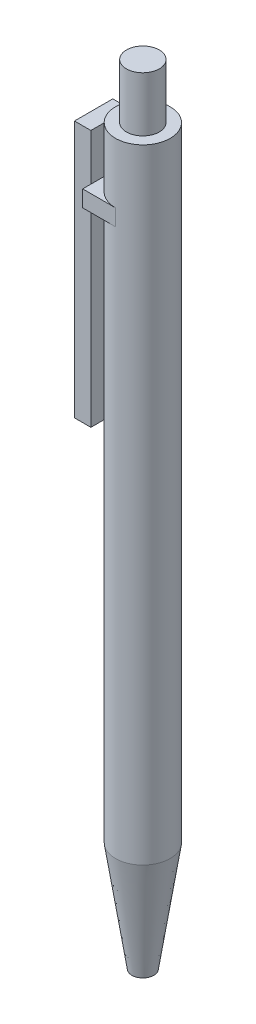
SolidWorks part; units mm, degrees
ref_plane "Plano frontal" through (0, 0, 0) normal (0, 0, 1) x (1, 0, 0)
ref_plane "Plano superior" through (0, 0, 0) normal (0, 1, 0) x (1, 0, 0)
ref_plane "Plano direito" through (0, 0, 0) normal (1, 0, 0) x (0, 0, -1)
sketch "Esboço2" plane through (0, 0, 0) normal (0, 0, 1) x (1, 0, 0)
  line L0 (-4.3308, 0) -> (2.3999, 0) construction
  line L1 (0, 22.7323) -> (0, -0.4304) construction
  line L2 (2, 0) -> (5, 20)
  line L3 (0, 0) -> (2, 0)
  line L4 (0, 20) -> (5, 20)
  line L5 (0, 20) -> (0, 0)
  point P9 (0, 0)
  point P11 (0, 0)
  dimension "D1" = 2
  dimension "D2" = 5
  dimension "D3" = 20
revolve "Revolução1" add sketch "Esboço2" angle 360 about L1
sketch "Esboço3" plane through (0, 20, 0) normal (0, 1, 0) x (1, 0, 0)
  line L0 (-21.4364, 0) -> (21.1711, 0) construction
  line L1 (0, 10.506) -> (0, -11.1957) construction
  circle A0 centre (0, 0) radius 5
  circle A1 centre (0, 0) radius 5 construction
  point P7 (0, 0)
  point P8 (0, 0)
extrude "Ressalto-extrusão1" add sketch "Esboço3" along normal blind 100
sketch "Esboço4" plane through (0, 120, 0) normal (0, 1, 0) x (1, 0, 0)
  line L0 (0, 11.0322) -> (0, -12.9913) construction
  line L1 (-16.4629, 0) -> (15.9617, 0) construction
  line L2 (-6, 5) -> (0, 5)
  line L3 (-6, 5) -> (-6, -5)
  line L4 (-6, -5) -> (0, -5)
  arc A0 (0, 5) -> (0, -5) centre (0, 0) cw
  circle A1 centre (0, 0) radius 5 construction
  point P8 (0, 0)
  point P10 (0, 0)
  point P15 (-6, 0)
  dimension "D1" = 6
extrude "Ressalto-extrusão2" add sketch "Esboço4" along normal blind 3
sketch "Esboço5" plane through (-6, 0, 0) normal (-1, 0, 0) x (0, 0, 1)
  line L0 (0, 126.2813) -> (0, 113.7617) construction
  line L1 (-5, 123) -> (5, 123) construction
  line L7 (-5, 123) -> (-5, 120) construction
  line L10 (-19.563, 121.5) -> (19.2509, 121.5) construction
  line L11 (-3.5, 131.5) -> (3.5, 131.5)
  line L12 (-3.5, 131.5) -> (-3.5, 84.5)
  line L13 (-3.5, 84.5) -> (3.5, 84.5)
  line L14 (3.5, 131.5) -> (3.5, 84.5)
  line L15 (-3.5, 131.5) -> (3.5, 84.5) construction
  line L16 (-3.5, 84.5) -> (3.5, 131.5) construction
  point P4 (0, 123)
  point P7 (0, 0)
  point P8 (-5, 121.5)
  point P9 (0, 121.5)
  point P11 (0, 108)
  dimension "D1" = 47
  dimension "D2" = 10
  dimension "D3" = 7
extrude "Ressalto-extrusão3" add sketch "Esboço5" along normal blind 3
sketch "Esboço6" plane through (0, 123, 0) normal (0, 1, 0) x (1, 0, 0)
  line L0 (-24.3537, 0) -> (32.0944, 0) construction
  line L1 (0, 13.196) -> (0, -14.5201) construction
  circle A0 centre (0, 0) radius 5
  arc A1 (0, -5) -> (0, 5) centre (0, 0) ccw construction
  point P4 (0, 0)
  point P6 (0, 0)
extrude "Ressalto-extrusão4" add sketch "Esboço6" along normal blind 11
sketch "Esboço7" plane through (0, 134, 0) normal (0, 1, 0) x (1, 0, 0)
  line L0 (0, 12.202) -> (0, -14.3829) construction
  line L1 (-20.1539, 0) -> (17.3947, 0) construction
  circle A0 centre (0, 0) radius 3
  point P2 (0, 0)
  dimension "D1" = 6
extrude "Ressalto-extrusão5" add sketch "Esboço7" along normal blind 10
